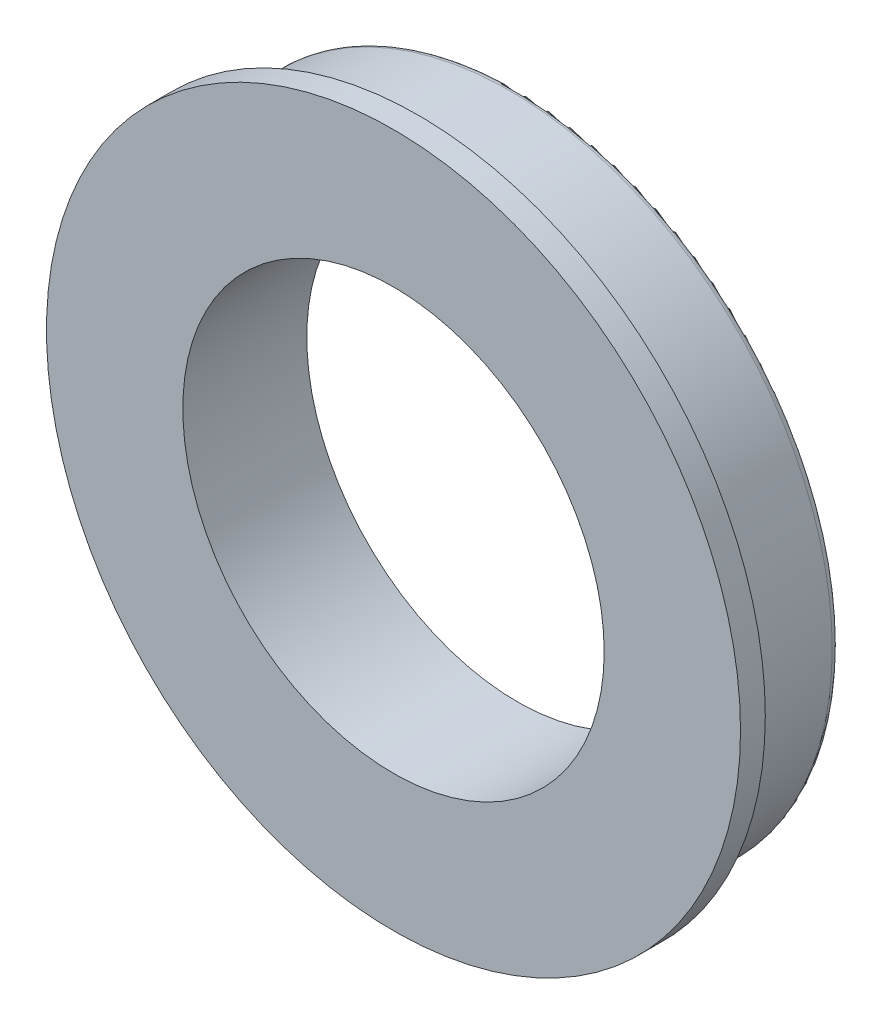
SolidWorks part; units mm, degrees
material "AISI 类型 A2 刀具钢"
ref_plane "前视基准面" through (0, 0, 0) normal (0, 0, 1) x (1, 0, 0)
ref_plane "上视基准面" through (0, 0, 0) normal (0, 1, 0) x (1, 0, 0)
ref_plane "右视基准面" through (0, 0, 0) normal (1, 0, 0) x (0, 0, -1)
sketch "草图1" plane through (0, 0, 0) normal (0, 0, 1) x (1, 0, 0)
  circle A0 centre (0, 0) radius 8.5
  circle A1 centre (0, 0) radius 13
extrude "凸台-拉伸1" add sketch "草图1" along normal blind 5
sketch "草图2" plane through (0, 0, 5) normal (0, 0, 1) x (1, 0, 0)
  circle A0 centre (0, 0) radius 14
  circle A1 centre (0, 0) radius 13
extrude "凸台-拉伸2" add sketch "草图2" against normal blind 1
fillet "圆角1" radius 0.3 1 edges at (13, 0, 0)
